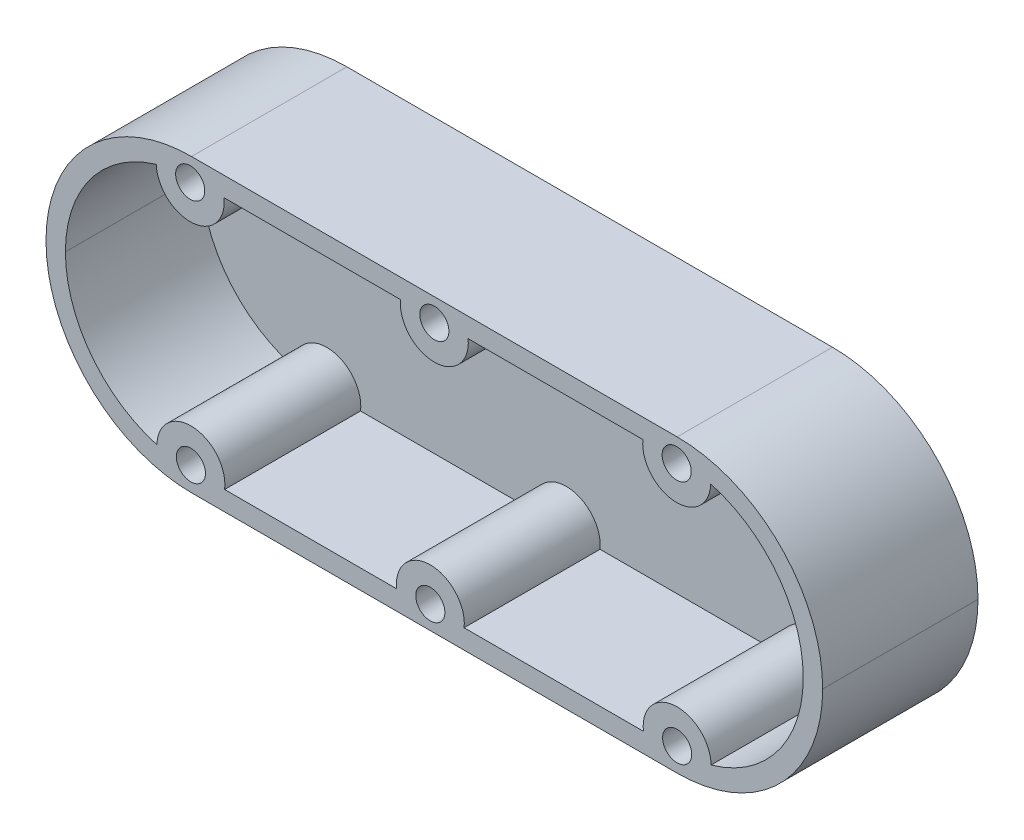
SolidWorks part; units mm, degrees
ref_plane "Front Plane" through (0, 0, 0) normal (0, 0, 1) x (1, 0, 0)
ref_plane "Top Plane" through (0, 0, 0) normal (0, 1, 0) x (1, 0, 0)
ref_plane "Right Plane" through (0, 0, 0) normal (1, 0, 0) x (0, 0, -1)
sketch "Sketch3" plane through (0, 0, 0) normal (0, 0, 1) x (1, 0, 0)
  line L5 (40.6057, -0.7849) -> (40.6057, -0.7649)
  line L6 (-24.4043, 14.2251) -> (25.6157, 14.2251)
  line L7 (-39.3943, -0.7849) -> (-39.3943, -0.7649)
  line L8 (-24.4043, -15.7749) -> (25.6157, -15.7749)
  circle A32 centre (25.5699, 11.8402) radius 1.5
  circle A33 centre (25.6157, -13.3549) radius 1.5
  circle A34 centre (0.1934, -13.4007) radius 1.5
  circle A35 centre (0.6057, 11.886) radius 1.5
  circle A36 centre (-24.5418, 11.8402) radius 1.5
  circle A37 centre (-24.4681, -13.3327) radius 1.5
  arc A38 (-39.3943, -0.7849) -> (-24.4043, -15.7749) centre (-24.4043, -0.7849) ccw
  arc A39 (-24.4043, 14.2251) -> (-39.3943, -0.7649) centre (-24.4043, -0.7649) ccw
  arc A40 (40.6057, -0.7649) -> (25.6157, 14.2251) centre (25.6157, -0.7649) ccw
  arc A41 (25.6157, -15.7749) -> (40.6057, -0.7849) centre (25.6157, -0.7849) ccw
  point P0 (0, 0)
extrude "Boss-Extrude2" add sketch "Sketch3" along normal blind 16 contours A38 L8 A41 L5 A40 L6 A39 L7 | A36 | A35 | A32 | A33 | A34 | A37
shell "Shell4" thickness 2
